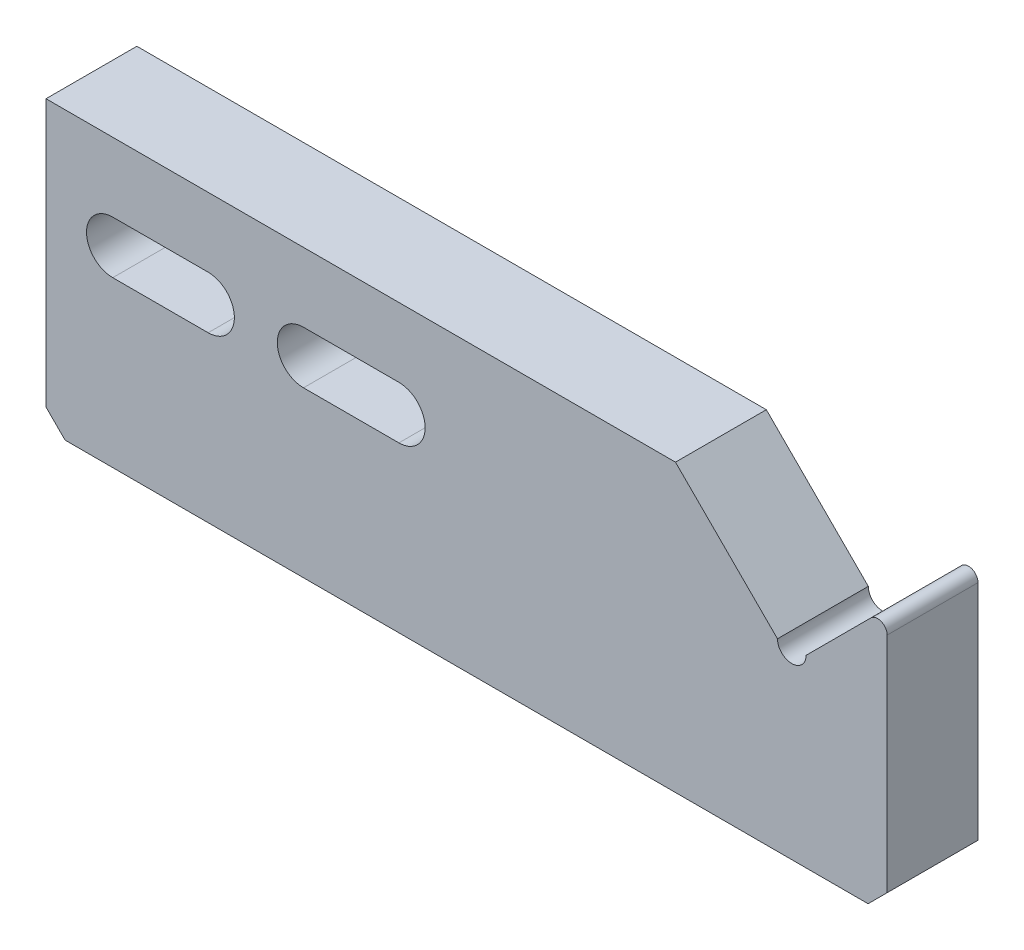
SolidWorks part; units mm, degrees
material "Plain Carbon Steel"
ref_plane "Front Plane" through (0, 0, 0) normal (0, 0, 1) x (1, 0, 0)
ref_plane "Top Plane" through (0, 0, 0) normal (0, 1, 0) x (1, 0, 0)
ref_plane "Right Plane" through (0, 0, 0) normal (1, 0, 0) x (0, 0, -1)
sketch "Sketch1" plane through (0, 0, 0) normal (0, 0, 1) x (1, 0, 0)
  line L9 (-10, 267.2189) -> (-18.5, 258.7189)
  line L10 (-10, 267.2189) -> (-10, 239.4113)
  line L11 (-10, 239.4113) -> (-98.1924, 239.4113)
  line L12 (-32.1924, 269.4113) -> (-21.5, 258.7189)
  line L13 (-98.1924, 269.4113) -> (-32.1924, 269.4113)
  line L14 (-98.1924, 239.4113) -> (-98.1924, 269.4113)
  line L15 (-81.1924, 262.1613) -> (-91.1924, 262.1613)
  line L16 (-61.1924, 262.1613) -> (-71.1924, 262.1613)
  line L17 (-77.3264, 249.4113) -> (-111.1924, 249.4113) construction
  line L19 (-78.1924, 250.9113) -> (-98.1924, 250.9113) construction
  line L22 (-61.1924, 256.6613) -> (-71.1924, 256.6613)
  line L23 (-81.1924, 256.6613) -> (-91.1924, 256.6613)
  arc A1 (-21.5, 258.7189) -> (-18.5, 258.7189) centre (-20, 258.7189) ccw
  arc A6 (-61.1924, 256.6613) -> (-61.1924, 262.1613) centre (-61.1924, 259.4113) ccw
  arc A7 (-71.1924, 262.1613) -> (-71.1924, 256.6613) centre (-71.1924, 259.4113) ccw
  arc A8 (-81.1924, 256.6613) -> (-81.1924, 262.1613) centre (-81.1924, 259.4113) ccw
  arc A9 (-91.1924, 262.1613) -> (-91.1924, 256.6613) centre (-91.1924, 259.4113) ccw
extrude "Boss-Extrude1" add sketch "Sketch1" along normal blind 6 and the other way blind 3.525
fillet "Fillet1" radius 1 1 edges at (-10, 267.2189, 1.2375)
chamfer "Chamfer1" distance 2 angle 45 2 edges at (-98.1924, 239.4113, 1.2375) (-10, 239.4113, 1.2375)
ref_plane "Plane1" through (0, 0, 1.2375) normal (0, 0, -1) x (-1, 0, 0)
sketch "Sketch3" plane through (0, 0, 1.2375) normal (0, 0, -1) x (-1, 0, 0)
  line L0 (98.1924, 250.9113) -> (78.1924, 250.9113)
  line L1 (78.1924, 250.9113) -> (77.3264, 249.4113)
  line L2 (77.3264, 249.4113) -> (98.1924, 249.4113)
  line L3 (98.1924, 249.4113) -> (98.1924, 250.9113)
  line L4 (98.1924, 249.4113) -> (111.1924, 249.4113) construction
revolve "Cut-Revolve1" cut sketch "Sketch3" angle 360 about L4
chamfer "Chamfer2" distance 0.5 angle 45 1 edges at (-98.1924, 249.4113, -0.2625)
